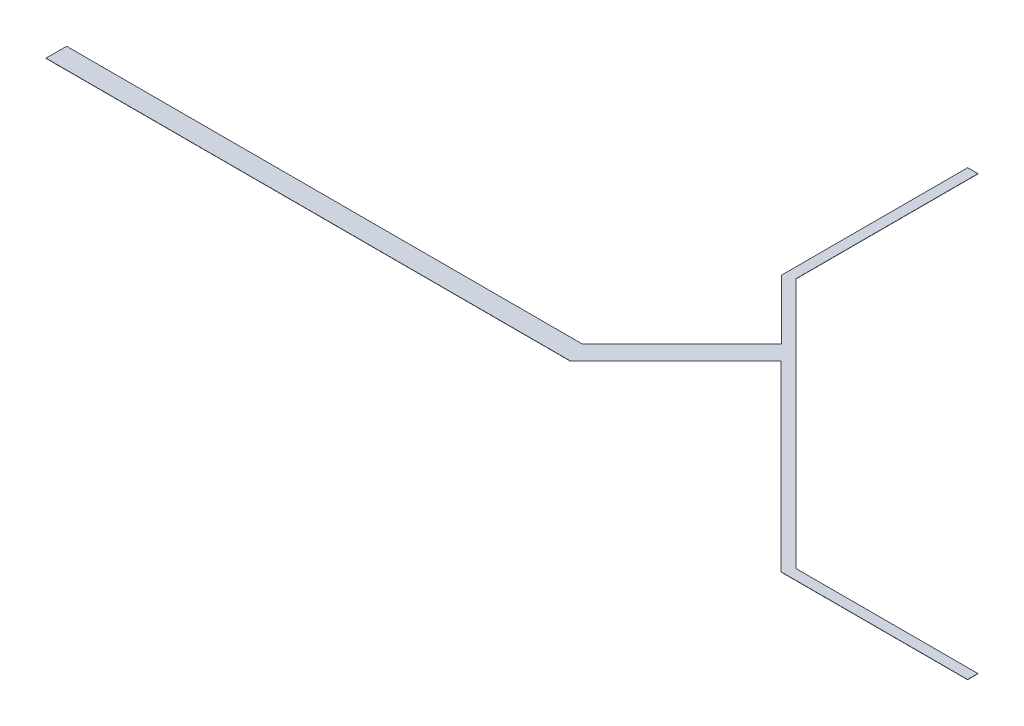
SolidWorks part; units mm, degrees
ref_plane "Front Plane" through (0, 0, 0) normal (0, 0, 1) x (1, 0, 0)
ref_plane "Top Plane" through (0, 0, 0) normal (0, 1, 0) x (1, 0, 0)
ref_plane "Right Plane" through (0, 0, 0) normal (1, 0, 0) x (0, 0, -1)
sketch "Sketch1" plane through (0, 0, 0) normal (0, 1, 0) x (1, 0, 0)
  line L0 (0, 0) -> (0, 2)
  line L1 (0, 0) -> (50.83, 0)
  line L2 (0, 2) -> (50, 2)
  line L3 (50, 2) -> (59.652, 11.652)
  line L4 (50.83, 0) -> (61.0618, 10.2318)
  line L5 (61.0618, 10.2318) -> (78.789, -7.4953)
  line L6 (59.652, 11.652) -> (53.8891, 17.4149)
  line L7 (78.789, -7.4953) -> (96.869, -7.4953)
  line L8 (53.8891, 17.4149) -> (53.8891, 35.4949)
  line L9 (53.8891, 35.4949) -> (54.8891, 35.4949)
  line L10 (96.869, -7.4953) -> (96.869, -6.4953)
  line L11 (96.869, -6.4953) -> (79.209, -6.4953)
  line L12 (54.8891, 35.4949) -> (54.8891, 17.8349)
  line L13 (54.8891, 17.8349) -> (79.209, -6.4953)
extrude "Boss-Extrude1" add sketch "Sketch1" along normal blind 0.02
scale "Scale1" scale about centroid uniform scaling yes scale factor 0.75
